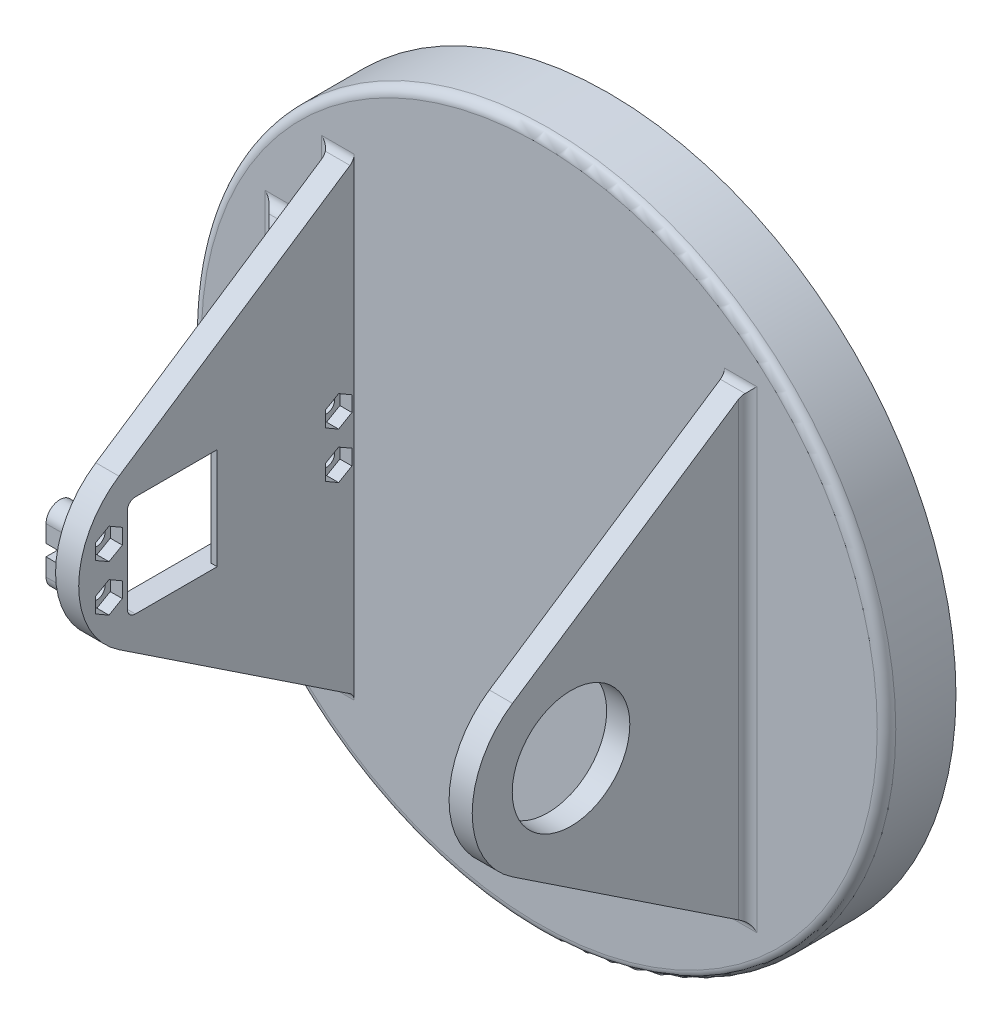
SolidWorks part; units mm, degrees
ref_plane "Front Plane" through (0, 0, 0) normal (0, 0, 1) x (1, 0, 0)
ref_plane "Top Plane" through (0, 0, 0) normal (0, 1, 0) x (1, 0, 0)
ref_plane "Right Plane" through (0, 0, 0) normal (1, 0, 0) x (0, 0, -1)
sketch "Sketch1" plane through (0, 0, 0) normal (0, 0, 1) x (1, 0, 0)
  circle A0 centre (0, 0) radius 75
  dimension "D1" = 150
extrude "Base Plate\\" add sketch "Sketch1" along normal blind 15
sketch "Sketch2" plane through (0, 0, 0) normal (0, 0, -1) x (-1, 0, 0)
  circle A0 centre (0, 0) radius 25 construction
  circle A1 centre (0, -25) radius 4.5
  circle A2 centre (-23.7764, -7.7254) radius 4.5
  circle A3 centre (-14.6946, 20.2254) radius 4.5
  circle A4 centre (14.6946, 20.2254) radius 4.5
  circle A5 centre (23.7764, -7.7254) radius 4.5
  point P16 (0, 0)
  dimension "D2" = 9
  dimension "D3" = 50
  dimension "D1" = 5
extrude "Drive Holes" cut sketch "Sketch2" against normal blind 10
chamfer "Chamfer1" distance 1 5 edges at (19.2764, -7.7254, 0) (10.1946, 20.2254, 0) (-19.1946, 20.2254, 0) (-28.2764, -7.7254, 0) (-4.5, -25, 0)
sketch "Sketch4" plane through (0, 0, 0) normal (1, 0, 0) x (0, 0, -1)
  line L0 (-15, 50) -> (-65.792, 16.2334)
  line L1 (-15, 75) -> (-15, -75) construction
  line L2 (-65.792, -16.2334) -> (-15, -50)
  line L3 (-15, -50) -> (-15, 50)
  arc A0 (-65.792, 16.2334) -> (-65.792, -16.2334) centre (-55, 0) ccw
  dimension "D1" = 100
  dimension "D2" = 40
extrude "Base Fin" add sketch "Sketch4" against normal blind 5 from offset 45
sketch "Sketch5" plane through (40, 0, 0) normal (-1, 0, 0) x (0, 0, 1)
  line L0 (15, 50) -> (15, -50)
  line L1 (15, -50) -> (65.792, -16.2334)
  line L2 (65.792, 16.2334) -> (15, 50)
  arc A0 (65.792, -16.2334) -> (65.792, 16.2334) centre (55, 0) ccw
extrude "Base Fin 2" add sketch "Sketch5" against normal blind 5 from offset 85
sketch "Sketch6" plane through (-45, 0, 0) normal (-1, 0, 0) x (0, 0, 1)
  line L0 (64, 8.8324) -> (64, -9.5676)
  line L1 (62.25, -11.3176) -> (24.05, -11.3176)
  line L2 (22.3, -9.5676) -> (22.3, 8.8324)
  line L3 (24.05, 10.5824) -> (62.25, 10.5824)
  arc A0 (64, -9.5676) -> (62.25, -11.3176) centre (62.25, -9.5676) cw
  arc A1 (24.05, -11.3176) -> (22.3, -9.5676) centre (24.05, -9.5676) cw
  arc A2 (22.3, 8.8324) -> (24.05, 10.5824) centre (24.05, 8.8324) cw
  arc A3 (62.25, 10.5824) -> (64, 8.8324) centre (62.25, 8.8324) cw
extrude "Cut-Extrude1" cut sketch "Sketch6" against normal up to next
sketch "Sketch7" plane through (-45, 0, 0) normal (-1, 0, 0) x (0, 0, 1)
  circle A0 centre (18.35, 4.6324) radius 1.75
  circle A1 centre (18.35, -5.3676) radius 1.75
  circle A2 centre (67.95, -5.3676) radius 1.75
  circle A3 centre (67.95, 4.6324) radius 1.75
  dimension "D1" = 3.5
extrude "Cut-Extrude2" cut sketch "Sketch7" against normal up to next
sketch "Sketch8" plane through (-45, 0, 0) normal (-1, 0, 0) x (0, 0, 1)
  line L0 (67.95, 4.6324) -> (67.95, -5.3676) construction
  line L1 (70.95, 4.6324) -> (70.95, -5.3676)
  line L2 (64.95, 4.6324) -> (64.95, -5.3676)
  line L3 (15, 7.6324) -> (15, 0)
  line L4 (15, -75) -> (15, 75) construction
  line L5 (15, 0) -> (15, -8.3676)
  line L6 (15, -8.3676) -> (18.35, -8.3676)
  line L7 (21.35, -5.3676) -> (21.35, 4.6324)
  line L8 (18.35, 7.6324) -> (15, 7.6324)
  arc A0 (70.95, 4.6324) -> (64.95, 4.6324) centre (67.95, 4.6324) ccw
  arc A1 (64.95, -5.3676) -> (70.95, -5.3676) centre (67.95, -5.3676) ccw
  arc A2 (18.35, -8.3676) -> (21.35, -5.3676) centre (18.35, -5.3676) ccw
  arc A3 (21.35, 4.6324) -> (18.35, 7.6324) centre (18.35, 4.6324) ccw
  circle A4 centre (18.35, 4.6324) radius 1.75 construction
  circle A5 centre (18.35, -5.3676) radius 1.75 construction
  point P4 (67.95, -0.3676)
  dimension "D1" = 3
  dimension "D2" = 3
extrude "Boss-Extrude1" add sketch "Sketch8" along normal up to surface (5.6 mm away)
sketch "Sketch9" plane through (-45, 0, 0) normal (1, 0, 0) x (0, 0, -1)
  circle A0 centre (-67.95, -5.3676) radius 1.75
  circle A1 centre (-67.95, 4.6324) radius 1.75
  circle A2 centre (-18.35, -5.3676) radius 1.75
  circle A3 centre (-18.35, 4.6324) radius 1.75
extrude "Cut-Extrude3" cut sketch "Sketch9" against normal up to surface (5.6 mm away) up to face at (-50.6, -0.3676, 18.4404)
sketch "Sketch10" plane through (-50.6, 0, 0) normal (-1, 0, 0) x (0, 0, 1)
  line L0 (21.35, 0.8824) -> (16.75, 0.8824)
  line L1 (21.35, 4.6324) -> (21.35, -5.3676) construction
  line L2 (16.75, 0.8824) -> (16.75, -1.6176)
  line L3 (16.75, -1.6176) -> (21.35, -1.6176)
  line L4 (23.05, 0.3824) -> (17.25, 0.3824) construction
  line L5 (17.25, -1.1176) -> (23.05, -1.1176) construction
  line L6 (17.25, 0.3824) -> (17.25, -1.1176) construction
  line L7 (21.35, 0.8824) -> (21.35, -1.6176)
  line L10 (64.95, -5.3676) -> (64.95, 4.6324) construction
  line L14 (64.95, -1.5747) -> (64.95, 0.9253)
  line L22 (64.95, 0.9253) -> (70.95, 0.9253)
  line L23 (70.95, 4.6324) -> (70.95, -5.3676) construction
  line L24 (70.95, 0.9253) -> (70.95, -1.5747)
  line L25 (70.95, -1.5747) -> (64.95, -1.5747)
  dimension "D1" = 0.5
  dimension "D2" = 0.5
  dimension "D3" = 0.5
extrude "Cut-Extrude4" cut sketch "Sketch10" against normal up to surface (5.6 mm away) up to face at (-45, -0.2206, 28.0928)
sketch "Sketch11" plane through (-40, 0, 0) normal (1, 0, 0) x (0, 0, -1)
  line L1 (-65.075, -7.0275) -> (-65.075, -3.7077)
  line L2 (-65.075, -3.7077) -> (-67.95, -2.0478)
  line L3 (-67.95, -2.0478) -> (-70.825, -3.7077)
  line L4 (-70.825, -3.7077) -> (-70.825, -7.0275)
  line L5 (-70.825, -7.0275) -> (-67.95, -8.6874)
  line L6 (-67.95, -8.6874) -> (-65.075, -7.0275)
  line L7 (-65.075, 2.9725) -> (-65.075, 6.2923)
  line L8 (-65.075, 6.2923) -> (-67.95, 7.9522)
  line L9 (-67.95, 7.9522) -> (-70.825, 6.2923)
  line L10 (-70.825, 6.2923) -> (-70.825, 2.9725)
  line L11 (-70.825, 2.9725) -> (-67.95, 1.3126)
  line L12 (-67.95, 1.3126) -> (-65.075, 2.9725)
  line L13 (-15.475, -7.0275) -> (-15.475, -3.7077)
  line L14 (-15.475, -3.7077) -> (-18.35, -2.0478)
  line L15 (-18.35, -2.0478) -> (-21.225, -3.7077)
  line L16 (-21.225, -3.7077) -> (-21.225, -7.0275)
  line L17 (-21.225, -7.0275) -> (-18.35, -8.6874)
  line L18 (-18.35, -8.6874) -> (-15.475, -7.0275)
  line L19 (-15.475, 2.9725) -> (-15.475, 6.2923)
  line L20 (-15.475, 6.2923) -> (-18.35, 7.9522)
  line L21 (-18.35, 7.9522) -> (-21.225, 6.2923)
  line L22 (-21.225, 6.2923) -> (-21.225, 2.9725)
  line L23 (-21.225, 2.9725) -> (-18.35, 1.3126)
  line L24 (-18.35, 1.3126) -> (-15.475, 2.9725)
  circle A0 centre (-67.95, -5.3676) radius 2.875 construction
  circle A1 centre (-67.95, 4.6324) radius 2.875 construction
  circle A2 centre (-18.35, -5.3676) radius 2.875 construction
  circle A3 centre (-18.35, 4.6324) radius 2.875 construction
  circle A4 centre (-18.35, 4.6324) radius 1.75 construction
  dimension "D1" = 5.75
extrude "Cut-Extrude5" cut sketch "Sketch11" against normal blind 2.6
sketch "Sketch12" plane through (-40, 0, 0) normal (1, 0, 0) x (0, 0, -1)
  line L0 (-44.5721, -11.3176) -> (-44.5721, 10.5824)
  line L1 (-62.25, -11.3176) -> (-24.05, -11.3176) construction
  line L2 (-24.05, 10.5824) -> (-62.25, 10.5824) construction
  line L3 (-44.5721, 10.5824) -> (-24.05, 10.5824)
  line L4 (-22.3, 8.8324) -> (-22.3, -9.5676)
  line L5 (-24.05, -11.3176) -> (-44.5721, -11.3176)
  arc A0 (-24.05, 10.5824) -> (-22.3, 8.8324) centre (-24.05, 8.8324) cw
  arc A1 (-22.3, -9.5676) -> (-24.05, -11.3176) centre (-24.05, -9.5676) cw
extrude "Boss-Extrude2" add sketch "Sketch12" against normal up to surface (1.38 mm away)
fillet "Fillet1" radius 2 9 edges at (42.5, -50, 15) (42.5, 50, 15) (45, 0, 15) (-47.8, 7.6324, 15) (-47.8, -8.3676, 15) (-42.5, -50, 15) (-42.5, 50, 15) (-45, -29.1838, 15) (-45, 28.8162, 15)
fillet "Fillet2" radius 2 1 edges at (75, 0, 15)
sketch "Sketch13" plane through (40, 0, 0) normal (-1, 0, 0) x (0, 0, 1)
  circle A0 centre (53.15, -0.3676) radius 12.7
  arc A1 (53.15, 19.6324) -> (53.15, -20.3676) centre (53.15, -0.3676) ccw construction
  dimension "D1" = 25.4
extrude "Cut-Extrude6" cut sketch "Sketch13" against normal up to next
sketch "Sketch14" plane through (40, 0, 0) normal (-1, 0, 0) x (0, 0, 1)
  line L1 (15.8928, 49.4065) -> (65.792, 16.2334) construction
  line L2 (33.6357, 37.6109) -> (32.6621, -38.2582)
  line L3 (65.792, -16.2334) -> (15.8928, -49.4065) construction
  line L4 (32.6621, -38.2582) -> (65.792, -16.2334)
  line L5 (65.792, 16.2334) -> (33.6357, 37.6109)
  arc A1 (65.792, -16.2334) -> (65.792, 16.2334) centre (55, 0) ccw
extrude "Cut-Extrude7" [suppressed] cut sketch "Sketch14" against normal blind 0.5
sketch "Sketch15" plane through (-60.2486, 10.197, -5.5394) normal (0, 1, 0) x (-1, 0, 0)
  line L0 (42.6672, 20.5394) -> (42.6672, 34.6818)
  line L1 (-107.2486, 20.5394) -> (-100.2486, 20.5394) construction
  line L2 (42.6672, 34.6818) -> (56.8096, 20.5394)
  line L3 (12.7514, 20.5394) -> (-133.2486, 20.5394) construction
  line L4 (56.8096, 20.5394) -> (42.6672, 20.5394)
  dimension "D1" = 45
extrude "Boss-Extrude3" [suppressed] add sketch "Sketch15" along normal mid plane 5
fillet "Fillet3" [suppressed] radius 2
sketch "Sketch17" plane through (0, 0, 0) normal (0, 1, 0) x (1, 0, 0)
  line L0 (-42.6672, -13) -> (-42.6672, -30.7242)
  line L1 (75, -13) -> (-75, -13) construction
  line L2 (-42.6672, -30.7242) -> (-60.3915, -13)
  line L3 (-60.3915, -13) -> (-42.6672, -13)
extrude "Boss-Extrude4" add sketch "Sketch17" along normal mid plane 5 from offset 20
sketch "Sketch18" plane through (-60.2486, 10.197, -5.5394) normal (0, 1, 0) x (-1, 0, 0)
  line L0 (-1.8571, 20.5394) -> (-15.2486, 33.9309)
  line L1 (-15.2486, 33.9309) -> (-15.2486, 20.5394)
  line L2 (-20.2486, 20.5394) -> (-13.2486, 20.5394) construction
  line L3 (-15.2486, 20.5394) -> (-1.8571, 20.5394)
extrude "Boss-Extrude5" add sketch "Sketch18" along normal mid plane 5 from offset 20
fillet "Fillet4" radius 2 16 edges at (-45, 17.5, 22.6957) (-45.5858, 17.5, 15.5858) (-45, 22.5, 22.6957) (-45.5858, 22.5, 15.5858) (-45, 27.697, 22.6957) (-45, 32.697, 22.6957) (-45, 20, 28.3915) (-58.3915, 20, 15) (-52.6957, 17.5, 15) (-52.6957, 22.5, 15) (-52.6957, 27.697, 15) (-58.3915, 30.197, 15) (-45, 30.197, 28.3915) (-52.6957, 32.697, 15) (-45.5858, 27.697, 15.5858) (-45.5858, 32.697, 15.5858)
